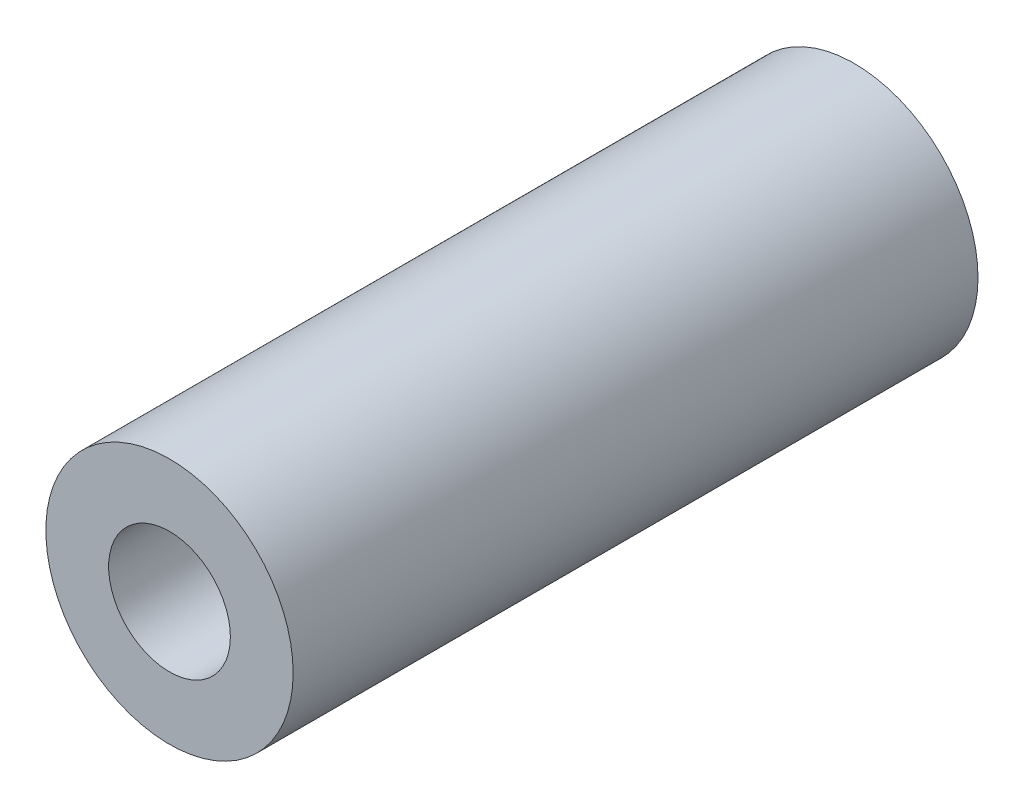
SolidWorks part; units mm, degrees
material "6063-O"
ref_plane "Plano frontal" through (0, 0, 0) normal (0, 0, 1) x (1, 0, 0)
ref_plane "Plano superior" through (0, 0, 0) normal (0, 1, 0) x (1, 0, 0)
ref_plane "Plano direito" through (0, 0, 0) normal (1, 0, 0) x (0, 0, -1)
sketch "Esboço1" plane through (0, 0, 0) normal (0, 0, 1) x (1, 0, 0)
  circle A0 centre (0, 0) radius 3.25
  circle A1 centre (0, 0) radius 1.6
  dimension "D1" = 6.5
  dimension "D2" = 3.2
extrude "Ressalto-extrusão1" add sketch "Esboço1" along normal blind 18
